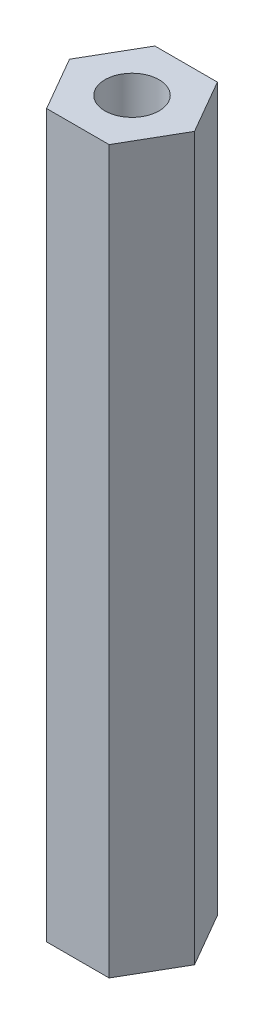
SolidWorks part; units mm, degrees
ref_plane "前基準面" through (0, 0, 0) normal (0, 0, 1) x (1, 0, 0)
ref_plane "上基準面" through (0, 0, 0) normal (0, 1, 0) x (1, 0, 0)
ref_plane "右基準面" through (0, 0, 0) normal (1, 0, 0) x (0, 0, -1)
sketch "草圖1" plane through (0, 0, 0) normal (0, 1, 0) x (1, 0, 0)
  line L1 (3.4641, 0) -> (1.7321, 3)
  line L2 (1.7321, 3) -> (-1.7321, 3)
  line L3 (-1.7321, 3) -> (-3.4641, 0)
  line L4 (-3.4641, 0) -> (-1.7321, -3)
  line L5 (-1.7321, -3) -> (1.7321, -3)
  line L6 (1.7321, -3) -> (3.4641, 0)
  circle A0 centre (0, 0) radius 3 construction
  circle A1 centre (0, 0) radius 1.5
  dimension "D2" = 3
  dimension "D1" = 6
extrude "填料-伸長1" add sketch "草圖1" along normal blind 40
